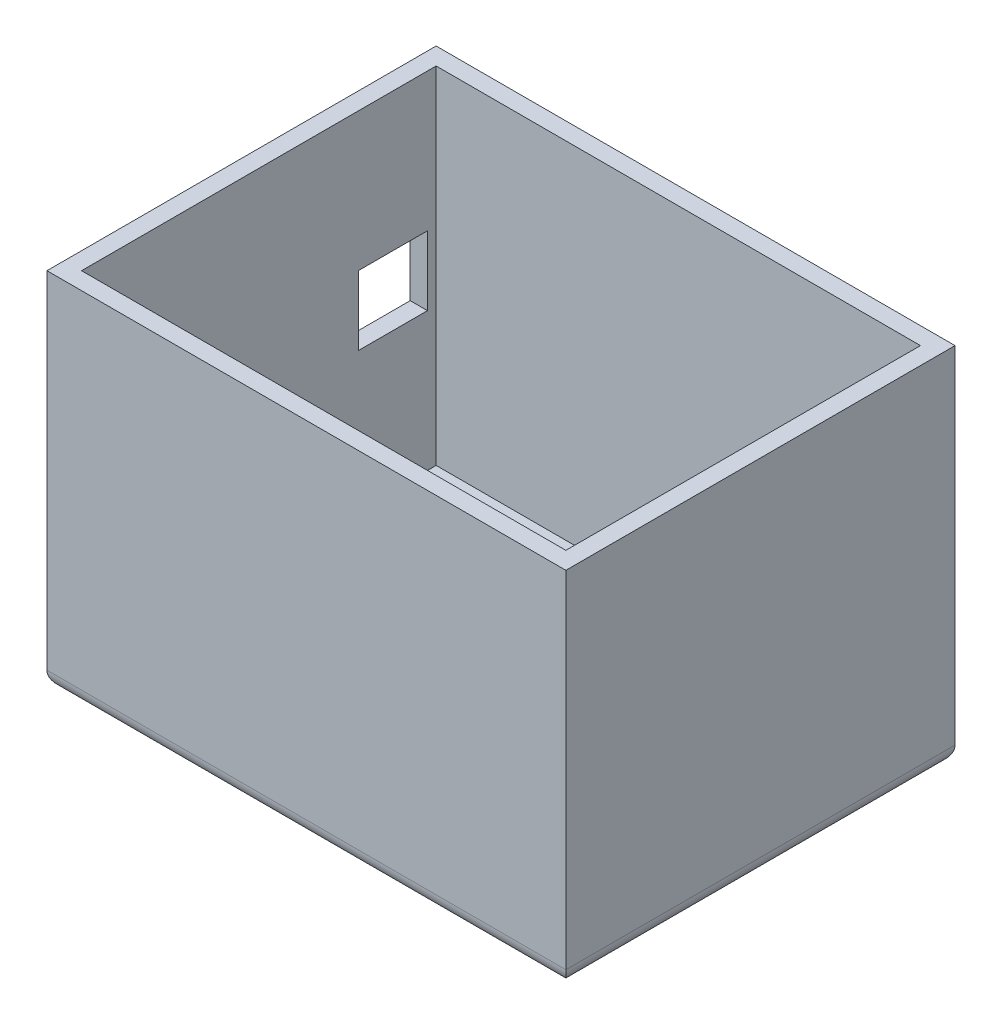
SolidWorks part; units mm, degrees
ref_plane "Front Plane" through (0, 0, 0) normal (0, 0, 1) x (1, 0, 0)
ref_plane "Top Plane" through (0, 0, 0) normal (0, 1, 0) x (1, 0, 0)
ref_plane "Right Plane" through (0, 0, 0) normal (1, 0, 0) x (0, 0, -1)
sketch "Sketch1" plane through (0, 0, 0) normal (0, 1, 0) x (1, 0, 0)
  line L0 (-300, -225) -> (-300, 225)
  line L1 (-280, -205) -> (280, -205)
  line L2 (-280, -205) -> (-280, 205)
  line L3 (-280, 205) -> (280, 205)
  line L4 (280, -205) -> (280, 205)
  line L5 (-280, -205) -> (280, 205) construction
  line L6 (-280, 205) -> (280, -205) construction
  line L7 (-300, 225) -> (300, 225)
  line L8 (300, -225) -> (300, 225)
  line L9 (-300, -225) -> (300, -225)
  point P0 (0, 0)
  dimension "D1" = 560
  dimension "D2" = 410
  dimension "D3" = 20
extrude "Boss-Extrude1" add sketch "Sketch1" along normal blind 400
sketch "Sketch2" plane through (0, 0, 0) normal (0, -1, 0) x (1, 0, 0)
  line L1 (-300, -225) -> (300, -225)
  line L2 (-300, -225) -> (-300, 225)
  line L3 (-300, 225) -> (300, 225)
  line L4 (300, -225) -> (300, 225)
  line L5 (-300, -225) -> (300, 225) construction
  line L6 (-300, 225) -> (300, -225) construction
  point P0 (0, 0)
extrude "Boss-Extrude2" add sketch "Sketch2" along normal blind 20
sketch "Sketch4" plane through (0, 0, 0) normal (0, 1, 0) x (1, 0, 0)
  line L0 (280, 205) -> (-280, 205) construction
  line L1 (-140, 205) -> (-130, 205)
  line L2 (-140, 205) -> (-140, -205)
  line L3 (-140, -205) -> (-130, -205)
  line L4 (-130, 205) -> (-130, -205)
  line L5 (-280, -205) -> (280, -205) construction
  dimension "D1" = 140
  dimension "D2" = 10
extrude "Boss-Extrude4" [suppressed] add sketch "Sketch4" along normal blind 350
sketch "Sketch5" [suppressed] plane through (0, 0, 0) normal (0, 1, 0) x (1, 0, 0)
  line L0 (280, 205) -> (-130, 205) construction
  line L1 (-140, -205) -> (-130, -205)
  line L2 (-140, -205) -> (-140, 205)
  line L3 (-140, 205) -> (-130, 205)
  line L4 (-130, -205) -> (-130, 205)
  line L5 (-130, 205) -> (-140, 205) construction
extrude "Cut-Extrude1" [suppressed] cut sketch "Sketch5" along normal blind 50
fillet "Fillet1" radius 20 4 edges at (0, -20, -225) (-300, -20, 0) (0, -20, 225) (300, -20, 0)
sketch "Sketch8" plane through (-300, 0, 0) normal (-1, 0, 0) x (0, 0, 1)
  line L0 (225, 400) -> (225, 0) construction
  line L1 (115, 240) -> (195, 240)
  line L2 (115, 240) -> (115, 160)
  line L3 (115, 160) -> (195, 160)
  line L4 (195, 240) -> (195, 160)
  line L5 (115, 240) -> (195, 160) construction
  line L6 (115, 160) -> (195, 240) construction
  line L7 (-195, 240) -> (-115, 240)
  line L8 (-195, 240) -> (-195, 160)
  line L9 (-195, 160) -> (-115, 160)
  line L10 (-115, 240) -> (-115, 160)
  line L11 (-195, 240) -> (-115, 160) construction
  line L12 (-195, 160) -> (-115, 240) construction
  line L13 (-225, 400) -> (225, 400) construction
  line L14 (-225, 400) -> (-225, 0) construction
  point P0 (155, 200)
  point P5 (-155, 200)
  dimension "D1" = 30
  dimension "D2" = 160
  dimension "D3" = 80
  dimension "D4" = 80
  dimension "D5" = 80
  dimension "D6" = 30
  dimension "D7" = 160
extrude "Cut-Extrude3" cut sketch "Sketch8" against normal up to surface (20 mm away) up to face at (-280, 200, 0)
